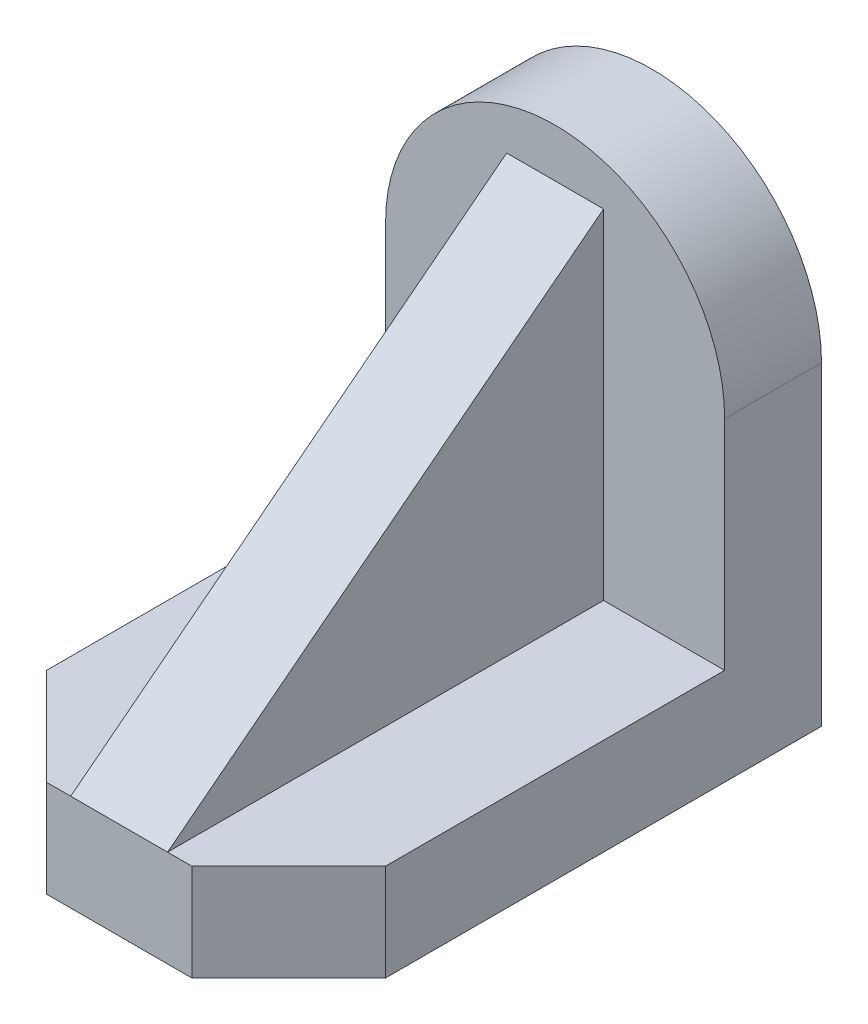
SolidWorks part; units mm, degrees
ref_plane "Alzado" through (0, 0, 0) normal (0, 0, 1) x (1, 0, 0)
ref_plane "Planta" through (0, 0, 0) normal (0, 1, 0) x (1, 0, 0)
ref_plane "Vista lateral" through (0, 0, 0) normal (1, 0, 0) x (0, 0, -1)
sketch "Sketch2" plane through (0, 0, 0) normal (0, 1, 0) x (1, 0, 0)
  line L17 (-21, -33) -> (21, -33)
  line L18 (-21, -33) -> (-21, 33)
  line L19 (-21, 33) -> (21, 33)
  line L20 (21, -33) -> (21, 33)
  line L21 (-21, -33) -> (21, 33) construction
  line L22 (-21, 33) -> (21, -33) construction
  point P0 (0, 0)
  dimension "D1" = 42
  dimension "D2" = 66
extrude "Boss-Extrude1" add sketch "Sketch2" along normal blind 12
chamfer "Chamfer1" distance 12 angle 45 2 edges at (-21, 6, 33) (21, 6, 33)
sketch "Sketch5" plane through (0, 12, 0) normal (0, 1, 0) x (1, 0, 0)
  line L0 (-21, 33) -> (-21, -21) construction
  line L1 (21, 33) -> (-21, 33)
  line L2 (21, 33) -> (21, 21)
  line L3 (21, 21) -> (-21, 21)
  line L4 (-21, 33) -> (-21, 21)
  dimension "D1" = 12
extrude "Boss-Extrude2" add sketch "Sketch5" along normal blind 27
sketch "Sketch6" plane through (0, 39, 0) normal (0, 1, 0) x (1, 0, 0)
  line L0 (-21, 21) -> (21, 21) construction
  line L1 (21, 33) -> (0, 33)
  line L2 (21, 33) -> (21, 21)
  line L3 (21, 21) -> (0, 21)
  line L4 (0, 33) -> (0, 21)
revolve "Revolve1" add sketch "Sketch6" angle 180 about L4
sketch "Sketch9" plane through (0, 0, 0) normal (1, 0, 0) x (0, 0, -1)
  line L0 (21, 12) -> (21, 54)
  line L1 (21, 60) -> (21, 39) construction
  line L2 (21, 54) -> (-33, 12)
  line L3 (-33, 12) -> (21, 12)
  dimension "D1" = 42
extrude "Boss-Extrude3" add sketch "Sketch9" along normal mid plane 12
